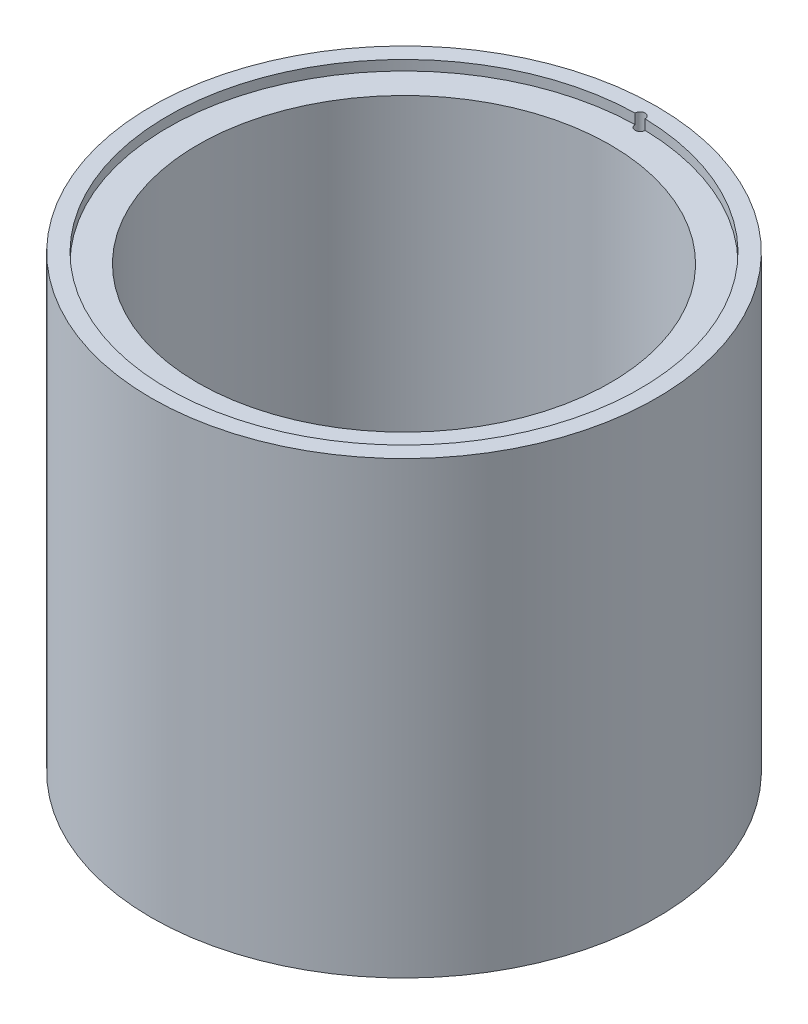
SolidWorks part; units mm, degrees
ref_plane "Front Plane" through (0, 0, 0) normal (0, 0, 1) x (1, 0, 0)
ref_plane "Top Plane" through (0, 0, 0) normal (0, 1, 0) x (1, 0, 0)
ref_plane "Right Plane" through (0, 0, 0) normal (1, 0, 0) x (0, 0, -1)
sketch "Sketch1" plane through (0, 0, 0) normal (0, 1, 0) x (1, 0, 0)
  circle A0 centre (0, 0) radius 20.625
  circle A1 centre (0, 0) radius 25.275
extrude "Boss-Extrude1" add sketch "Sketch1" along normal blind 45
sketch "Sketch2" plane through (0, 0, 0) normal (0, -1, 0) x (1, 0, 0)
  circle A0 centre (0, 0) radius 22.625
extrude "Cut-Extrude1" cut sketch "Sketch2" against normal blind 3.5
sketch "Sketch3" plane through (0, 45, 0) normal (0, 1, 0) x (1, 0, 0)
  circle A0 centre (0, 0) radius 23.625
extrude "Cut-Extrude2" cut sketch "Sketch3" against normal blind 1
sketch "Sketch4" plane through (0, 45, 0) normal (0, 1, 0) x (1, 0, 0)
  circle A0 centre (0, 23.625) radius 0.5
  circle A1 centre (0, 0) radius 23.625 construction
  circle A2 centre (0, 0) radius 23.625 construction
extrude "Cut-Extrude3" cut sketch "Sketch4" against normal blind 47.5
